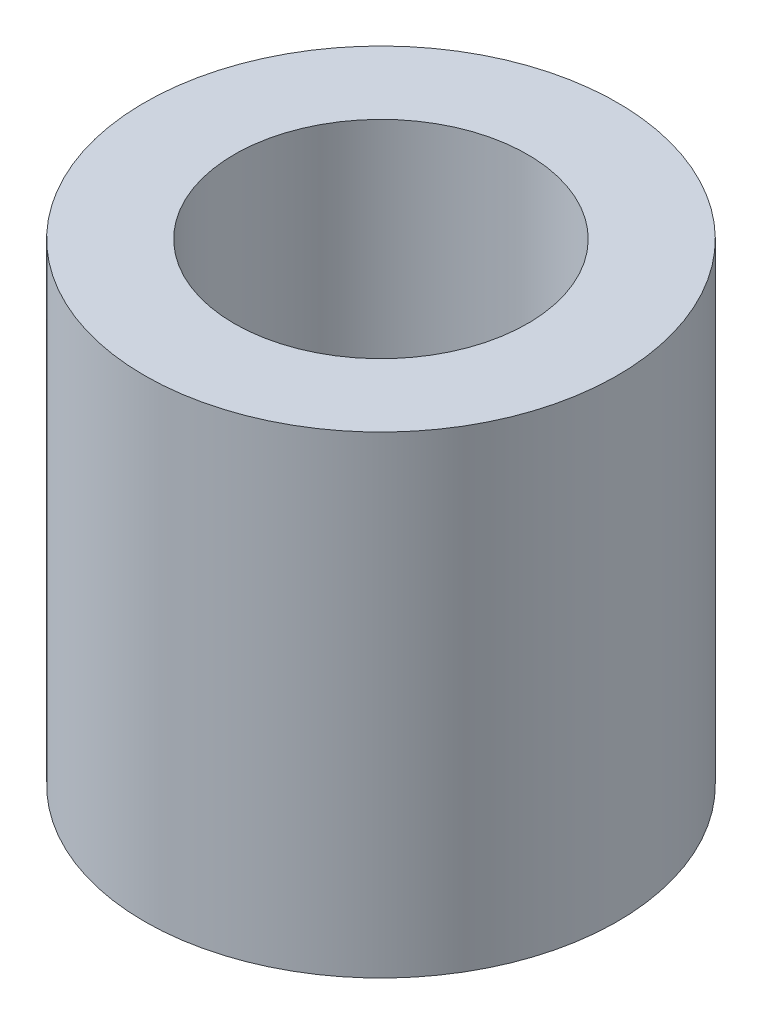
SolidWorks part; units mm, degrees
material "6061 合金"
ref_plane "前视基准面" through (0, 0, 0) normal (0, 0, 1) x (1, 0, 0)
ref_plane "上视基准面" through (0, 0, 0) normal (0, 1, 0) x (1, 0, 0)
ref_plane "右视基准面" through (0, 0, 0) normal (1, 0, 0) x (0, 0, -1)
sketch "草图1" plane through (0, 0, 0) normal (0, 1, 0) x (1, 0, 0)
  circle A0 centre (0, 0) radius 1.55
  circle A1 centre (0, 0) radius 2.5
  dimension "D1" = 5
  dimension "D2" = 3.1
extrude "凸台-拉伸1" add sketch "草图1" along normal blind 5
